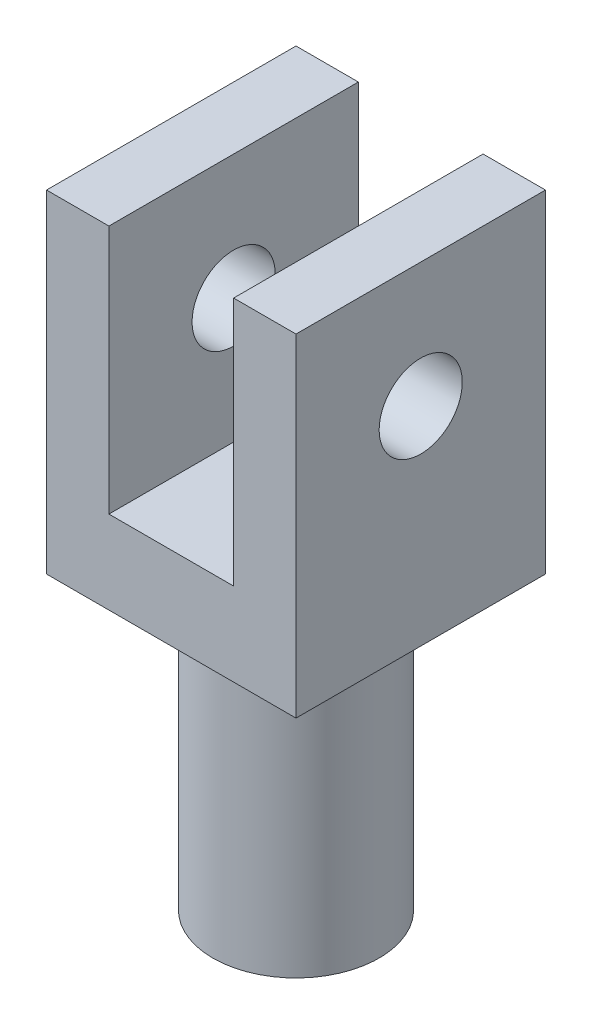
SolidWorks part; units mm, degrees
ref_plane "Plan de face" through (0, 0, 0) normal (0, 0, 1) x (1, 0, 0)
ref_plane "Plan de dessus" through (0, 0, 0) normal (0, 1, 0) x (1, 0, 0)
ref_plane "Plan de droite" through (0, 0, 0) normal (1, 0, 0) x (0, 0, -1)
sketch "Esquisse1" plane through (0, 0, 0) normal (0, 0, 1) x (1, 0, 0)
  line L1 (0, 0) -> (-30, 0)
  line L2 (0, 0) -> (0, 40)
  line L3 (0, 40) -> (-30, 40)
  line L4 (-30, 0) -> (-30, 40)
  dimension "D1" = 30
  dimension "D2" = 40
extrude "Boss.-Extru.1" add sketch "Esquisse1" along normal blind 30
sketch "Esquisse2" plane through (0, 0, 30) normal (0, 0, 1) x (1, 0, 0)
  line L0 (-22.5, 40) -> (-22.5, 10)
  line L1 (0, 40) -> (-30, 40) construction
  line L2 (-22.5, 10) -> (-7.5, 10)
  line L3 (-7.5, 10) -> (-7.5, 40)
  line L4 (-7.5, 40) -> (-22.5, 40)
  line L5 (-30, 40) -> (-30, 0) construction
  dimension "D1" = 15
  dimension "D2" = 7.5
  dimension "D3" = 30
extrude "Enlèv. mat.-Extru.1" cut sketch "Esquisse2" against normal blind 30
sketch "Esquisse3" plane through (-30, 0, 0) normal (-1, 0, 0) x (0, 0, 1)
  line L0 (30, 40) -> (0, 40) construction
  line L1 (0, 40) -> (0, 0) construction
  circle A0 centre (15, 25) radius 5
  dimension "D1" = 10
  dimension "D3" = 15
  dimension "D2" = 15
extrude "Enlèv. mat.-Extru.2" cut sketch "Esquisse3" against normal blind 50
sketch "Esquisse4" plane through (0, 0, 0) normal (0, -1, 0) x (1, 0, 0)
  line L1 (-30, 30) -> (-30, 0) construction
  line L2 (-30, 30) -> (0, 30) construction
  circle A0 centre (-15, 15) radius 10
  dimension "D1" = 15
  dimension "D2" = 15
extrude "Boss.-Extru.2" add sketch "Esquisse4" along normal blind 35
